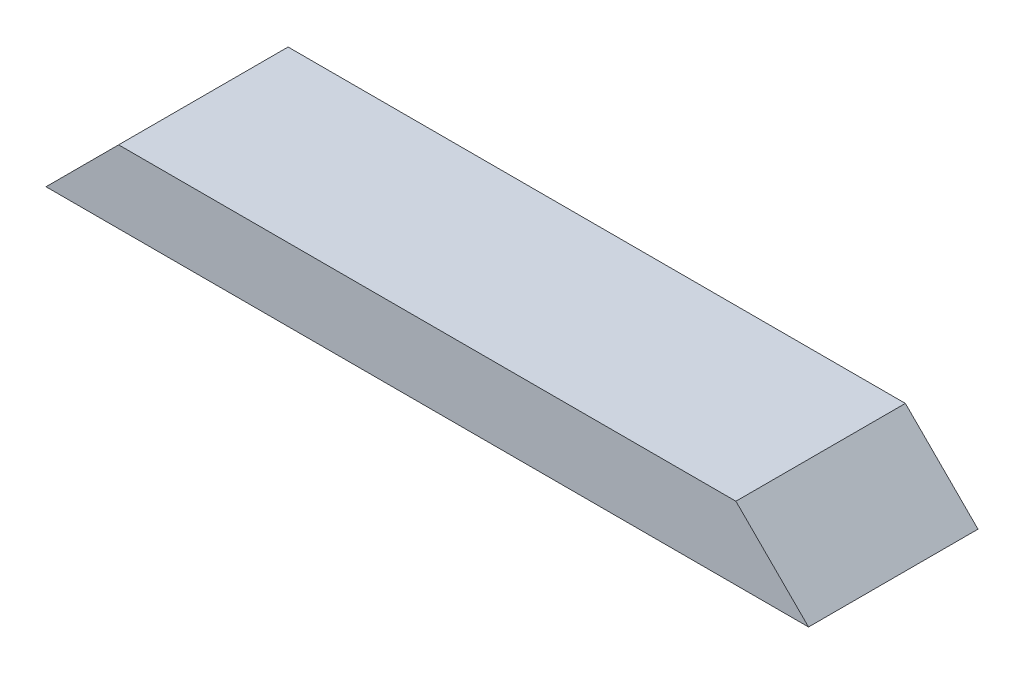
SolidWorks part; units mm, degrees
ref_plane "Front Plane" through (0, 0, 0) normal (0, 0, 1) x (1, 0, 0)
ref_plane "Top Plane" through (0, 0, 0) normal (0, 1, 0) x (1, 0, 0)
ref_plane "Right Plane" through (0, 0, 0) normal (1, 0, 0) x (0, 0, -1)
sketch "Sketch1" plane through (0, 0, 0) normal (0, 1, 0) x (1, 0, 0)
  line L1 (0, 0) -> (400.05, 0)
  line L2 (0, 0) -> (0, 88.9)
  line L3 (0, 88.9) -> (400.05, 88.9)
  line L4 (400.05, 0) -> (400.05, 88.9)
  dimension "D1" = 88.9
  dimension "D2" = 400.05
extrude "Boss-Extrude1" add sketch "Sketch1" along normal blind 38.1
sketch "Sketch2" plane through (0, 0, 0) normal (0, 0, 1) x (1, 0, 0)
  line L0 (0, 0) -> (38.1, 38.1)
  line L1 (0, 38.1) -> (400.05, 38.1) construction
  line L2 (38.1, 38.1) -> (0, 38.1)
  line L3 (0, 38.1) -> (0, 0)
  line L5 (400.05, 0) -> (400.05, 38.1)
  line L9 (400.05, 38.1) -> (361.95, 38.1)
  line L10 (361.95, 38.1) -> (400.05, 0)
  dimension "D1" = 38.1
  dimension "D2" = 38.1
  dimension "D3" = 38.1
extrude "Cut-Extrude1" cut sketch "Sketch2" against normal through all
